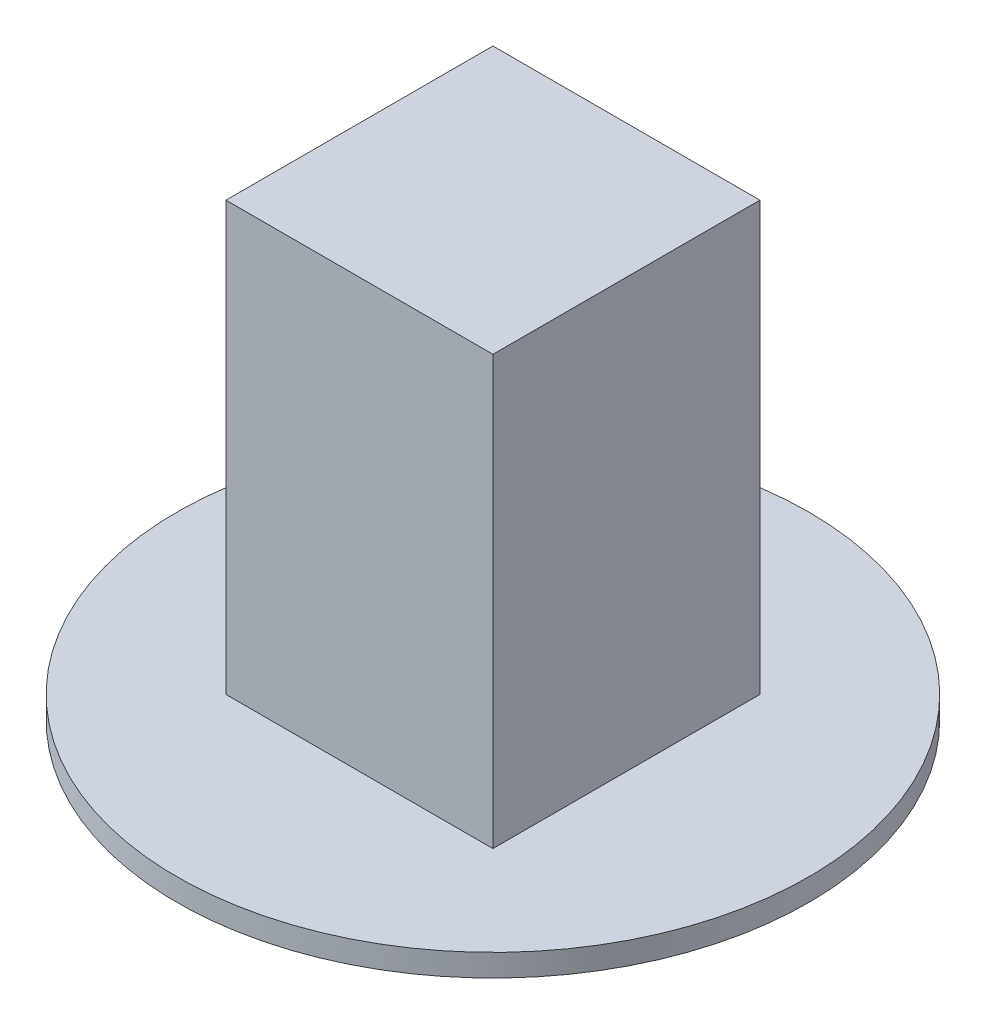
SolidWorks part; units mm, degrees
ref_plane "Front Plane" through (0, 0, 0) normal (0, 0, 1) x (1, 0, 0)
ref_plane "Top Plane" through (0, 0, 0) normal (0, 1, 0) x (1, 0, 0)
ref_plane "Right Plane" through (0, 0, 0) normal (1, 0, 0) x (0, 0, -1)
sketch "Sketch1" plane through (0, 0, 0) normal (0, 1, 0) x (1, 0, 0)
  line L0 (0, 24.4545) -> (0, -36.1592) construction
  line L1 (-19.05, 19.05) -> (19.05, 19.05)
  line L2 (-19.05, 19.05) -> (-19.05, -19.05)
  line L3 (-19.05, -19.05) -> (19.05, -19.05)
  line L4 (19.05, 19.05) -> (19.05, -19.05)
  line L5 (-28.366, 0) -> (29.2618, 0) construction
  dimension "D1" = 38.1
extrude "Boss-Extrude1" add sketch "Sketch1" along normal blind 61.087
sketch "Sketch2" plane through (0, 0, 0) normal (0, -1, 0) x (1, 0, 0)
  circle A0 centre (0, 0) radius 45.085
  dimension "D1" = 90.17
extrude "Boss-Extrude2" add sketch "Sketch2" along normal blind 3.175
